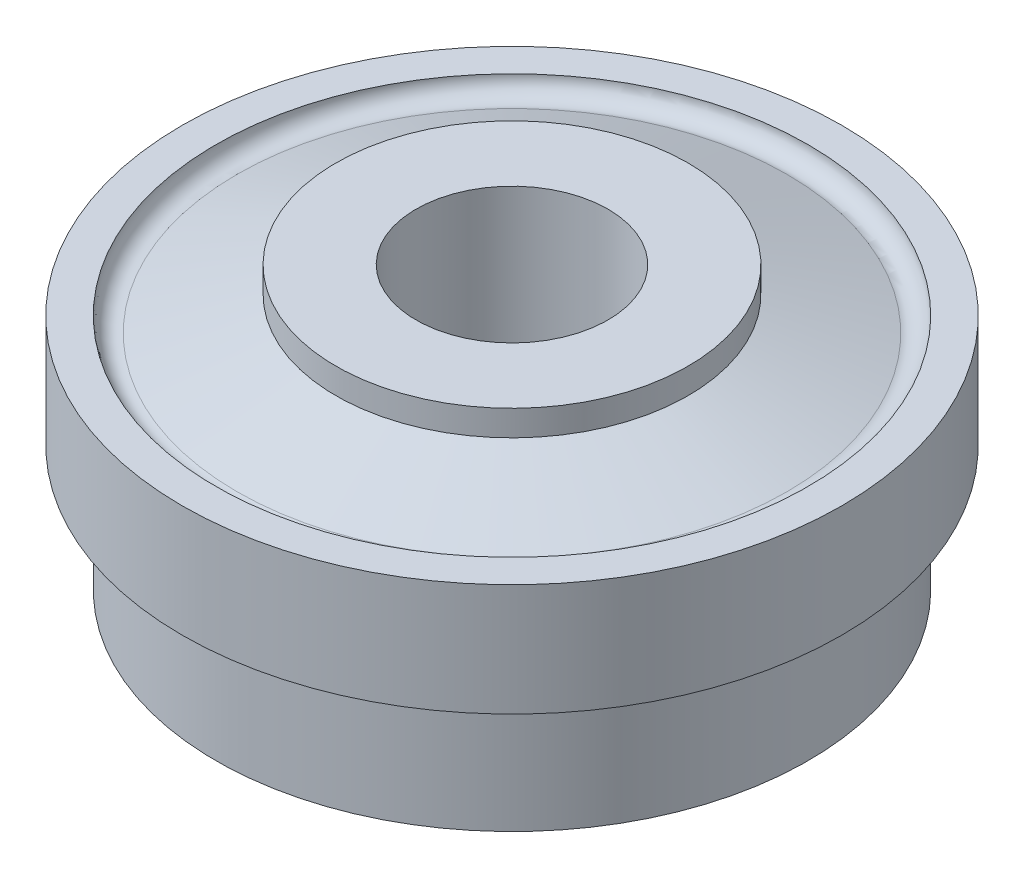
SolidWorks part; units mm, degrees
ref_plane "Front Plane" through (0, 0, 0) normal (0, 0, 1) x (1, 0, 0)
ref_plane "Top Plane" through (0, 0, 0) normal (0, 1, 0) x (1, 0, 0)
ref_plane "Right Plane" through (0, 0, 0) normal (1, 0, 0) x (0, 0, -1)
sketch "Sketch1" plane through (0, 0, 0) normal (0, 0, 1) x (1, 0, 0)
  line L0 (0, 0) -> (55, 0)
  line L1 (55, 0) -> (55, 45)
  line L2 (0, -19.7924) -> (0, 25.2031) construction
  line L3 (64.2594, 50.0375) -> (87.5, 35)
  line L4 (87.5, 35) -> (87.5, -12)
  line L5 (92.5, -12) -> (92.5, 27.2064)
  line L6 (92.5, 27.2064) -> (103, 27.2064)
  line L7 (103, 27.2064) -> (103, 62.2064)
  line L8 (103, 62.2064) -> (92.5, 62.2064)
  line L9 (0, 76) -> (55, 76)
  line L10 (55, 76) -> (55, 68)
  line L11 (55, 68) -> (85.8871, 57.4737)
  line L12 (87.5, -12) -> (92.5, -12)
  line L13 (92.5, 62.2064) -> (72, 62.2064) construction
  line L14 (30, 76) -> (30, 0)
  line L15 (87.5, 62.2064) -> (87.5, 57.2064) construction
  arc A1 (85.8871, 57.4737) -> (92.5, 62.2064) centre (87.5, 62.2064) ccw
  arc A2 (64.2594, 50.0375) -> (55, 45) centre (61, 45) ccw
  point P5 (55, 56.1644)
  point P7 (55.7979, 56.1644)
  dimension "D4" = 6
  dimension "D8" = 10
  dimension "D16" = 30.8871
  dimension "D1" = 185
  dimension "D2" = 12
  dimension "D3" = 47
  dimension "D5" = 10
  dimension "D6" = 110
  dimension "D7" = 185
  dimension "D9" = 60
  dimension "D10" = 206
  dimension "D11" = 110
  dimension "D12" = 8
  dimension "D13" = 35
  dimension "D14" = 88
  dimension "D15" = 5
revolve "Revolve1" add sketch "Sketch1" angle 360 about L2
